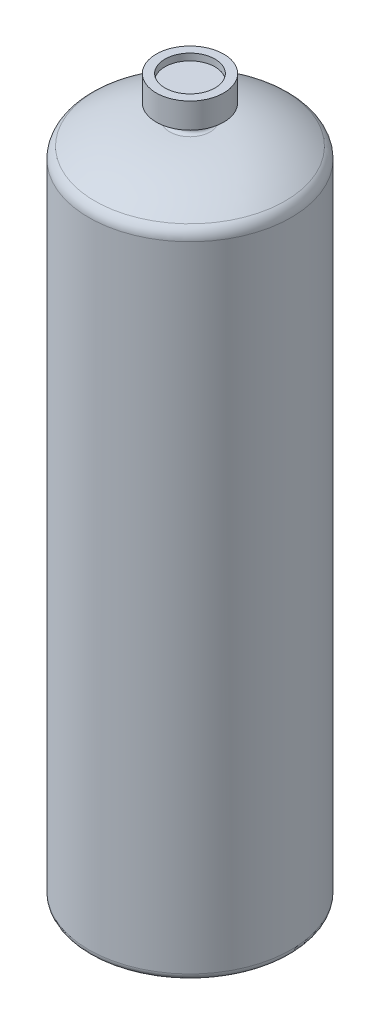
SolidWorks part; units mm, degrees
ref_plane "Front Plane" through (0, 0, 0) normal (0, 0, 1) x (1, 0, 0)
ref_plane "Top Plane" through (0, 0, 0) normal (0, 1, 0) x (1, 0, 0)
ref_plane "Right Plane" through (0, 0, 0) normal (1, 0, 0) x (0, 0, -1)
sketch "Sketch1" plane through (0, 0, 0) normal (0, 0, 1) x (1, 0, 0)
  line L0 (0, 0) -> (0, 269.24) construction
  line L1 (0, 0) -> (-38.1, 0)
  line L2 (-38.1, 0) -> (-38.1, 241.3)
  line L3 (-6.35, 255.27) -> (-6.35, 259.715)
  line L4 (-6.35, 259.715) -> (-12.7, 259.715)
  line L5 (-12.7, 259.715) -> (-12.7, 269.24)
  line L6 (-12.7, 269.24) -> (0, 269.24)
  line L7 (-7.62, 254) -> (0, 254) construction
  line L8 (0, 0) -> (0, 269.24)
  arc A0 (-38.1, 241.3) -> (-35.8163, 245.5411) centre (-33.02, 241.3) cw
  arc A1 (-35.8163, 245.5411) -> (-7.62, 254) centre (-7.62, 202.7767) cw
  arc A2 (-7.62, 254) -> (-6.35, 255.27) centre (-7.62, 255.27) ccw
  dimension "D2" = 1.27
  dimension "D9" = 5.08
  dimension "D1" = 241.3
  dimension "D3" = 15.24
  dimension "D4" = 25.4
  dimension "D5" = 12.7
  dimension "D6" = 9.525
  dimension "D7" = 12.7
  dimension "D8" = 76.2
revolve "Revolve1" add sketch "Sketch1" angle 360 about L8
fillet "Fillet1" radius 2.54 1 edges at (0, 0, -38.1)
sketch "Sketch2" plane through (0, 269.24, 0) normal (0, 1, 0) x (1, 0, 0)
  circle A0 centre (0, 0) radius 9.4268
extrude "Cut-Extrude1" cut sketch "Sketch2" against normal blind 2.54
